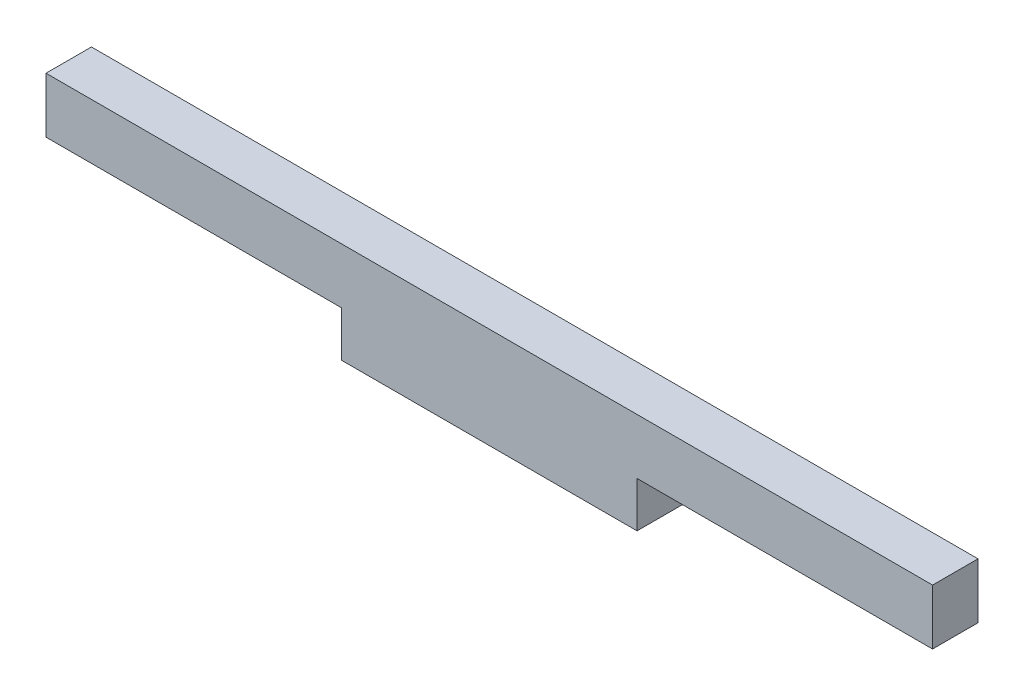
SolidWorks part; units mm, degrees
ref_plane "Front Plane" through (0, 0, 0) normal (0, 0, 1) x (1, 0, 0)
ref_plane "Top Plane" through (0, 0, 0) normal (0, 1, 0) x (1, 0, 0)
ref_plane "Right Plane" through (0, 0, 0) normal (1, 0, 0) x (0, 0, -1)
sketch "Sketch1" plane through (0, 0, 0) normal (0, 0, 1) x (1, 0, 0)
  line L0 (67.7333, 0) -> (101.6, 0)
  line L1 (0, 0) -> (33.8667, 0)
  line L2 (0, 0) -> (0, 6.35)
  line L3 (0, 6.35) -> (101.6, 6.35)
  line L4 (101.6, 0) -> (101.6, 6.35)
  line L6 (33.8667, 0) -> (33.8667, -5.207)
  line L7 (33.8667, -5.207) -> (67.7333, -5.207)
  line L8 (67.7333, 0) -> (67.7333, -5.207)
  dimension "D1" = 101.6
  dimension "D2" = 6.35
  dimension "D3" = 5.207
extrude "Boss-Extrude1" add sketch "Sketch1" along normal blind 5.207
equation "\"mat\" = \"mat2@jaws.assembly\""
equation "\"D3@Sketch1\"= \"mat\""
equation "\"D1@Boss-Extrude1\"= \"mat\""
